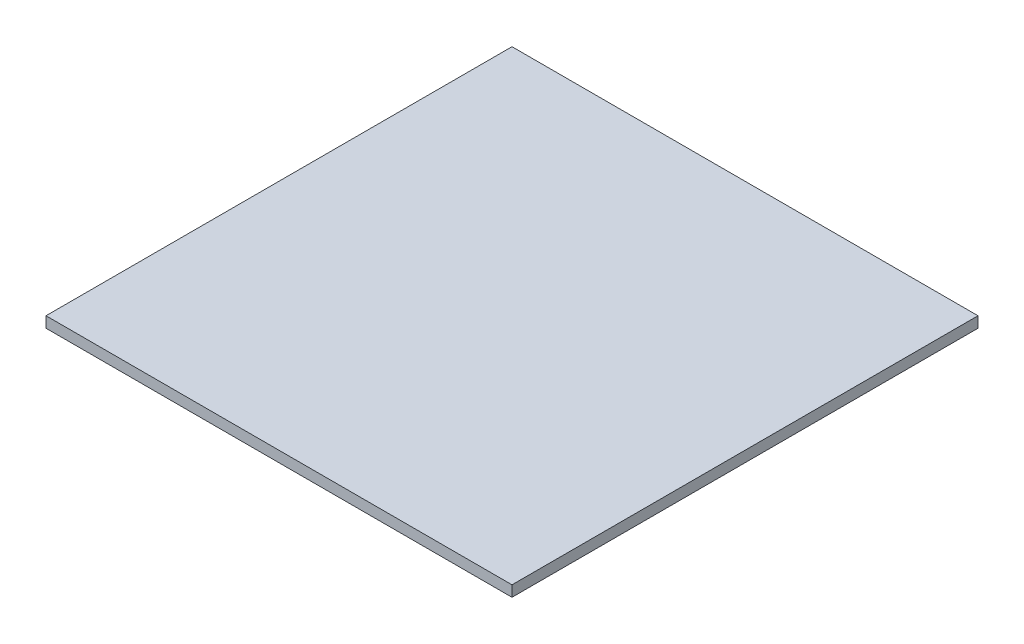
SolidWorks part; units mm, degrees
material "6061 Alloy"
ref_plane "Front Plane" through (0, 0, 0) normal (0, 0, 1) x (1, 0, 0)
ref_plane "Top Plane" through (0, 0, 0) normal (0, 1, 0) x (1, 0, 0)
ref_plane "Right Plane" through (0, 0, 0) normal (1, 0, 0) x (0, 0, -1)
sketch "Sketch1" plane through (0, 0, 0) normal (0, 1, 0) x (1, 0, 0)
  line L1 (-215, -215) -> (215, -215)
  line L2 (-215, -215) -> (-215, 215)
  line L3 (-215, 215) -> (215, 215)
  line L4 (215, -215) -> (215, 215)
  line L5 (-215, -215) -> (215, 215) construction
  line L6 (-215, 215) -> (215, -215) construction
  point P0 (0, 0)
extrude "Boss-Extrude1" add sketch "Sketch1" along normal blind 10 from offset 0
